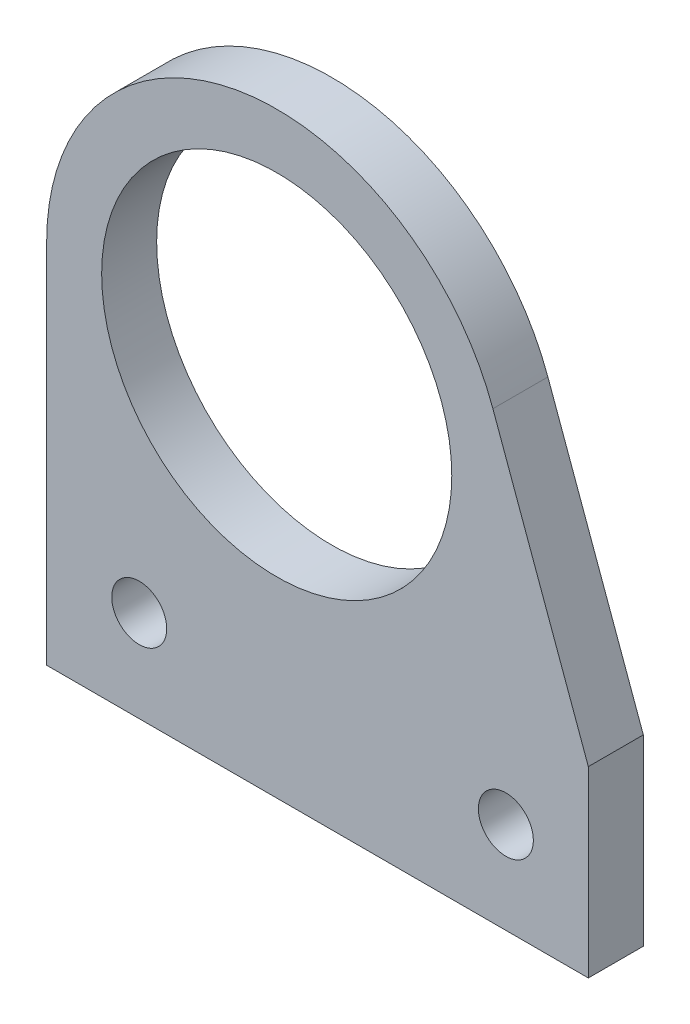
SolidWorks part; units mm, degrees
ref_plane "前视基准面" through (0, 0, 0) normal (0, 0, 1) x (1, 0, 0)
ref_plane "上视基准面" through (0, 0, 0) normal (0, 1, 0) x (1, 0, 0)
ref_plane "右视基准面" through (0, 0, 0) normal (1, 0, 0) x (0, 0, -1)
other "Configuration Table"
sketch "草图1" plane through (0, 0, 0) normal (0, 0, 1) x (1, 0, 0)
  line L1 (-12.55, -20) -> (17, -20)
  line L3 (-12.55, -15) -> (17, -15) construction
  line L4 (11.7931, 4.2924) -> (17, -10.0134)
  line L5 (17, -10.0134) -> (17, -20)
  line L7 (-12.55, -20) -> (-12.55, 0)
  circle A0 centre (0, 0) radius 9.55
  arc A1 (11.7931, 4.2924) -> (-12.55, 0) centre (0, 0) ccw
  circle A2 centre (-7.5, -15) radius 1.5
  circle A3 centre (12.5, -15) radius 1.5
  circle A4 centre (-7.5, -15) radius 2.5 construction
  circle A5 centre (12.5, -15) radius 2.5 construction
  circle A6 centre (0, 0) radius 5.05 construction
  dimension "D1" = 19.1
  dimension "D2" = 7.5
  dimension "D3" = 20
  dimension "D5" = 3
  dimension "D6" = 20
  dimension "D8" = 5
  dimension "D4" = 3
  dimension "D11" = 2
  dimension "D10" = 10.1
  dimension "D7" = 5
  dimension "D9" = 160
extrude "凸台-拉伸1" add sketch "草图1" along normal blind 3
